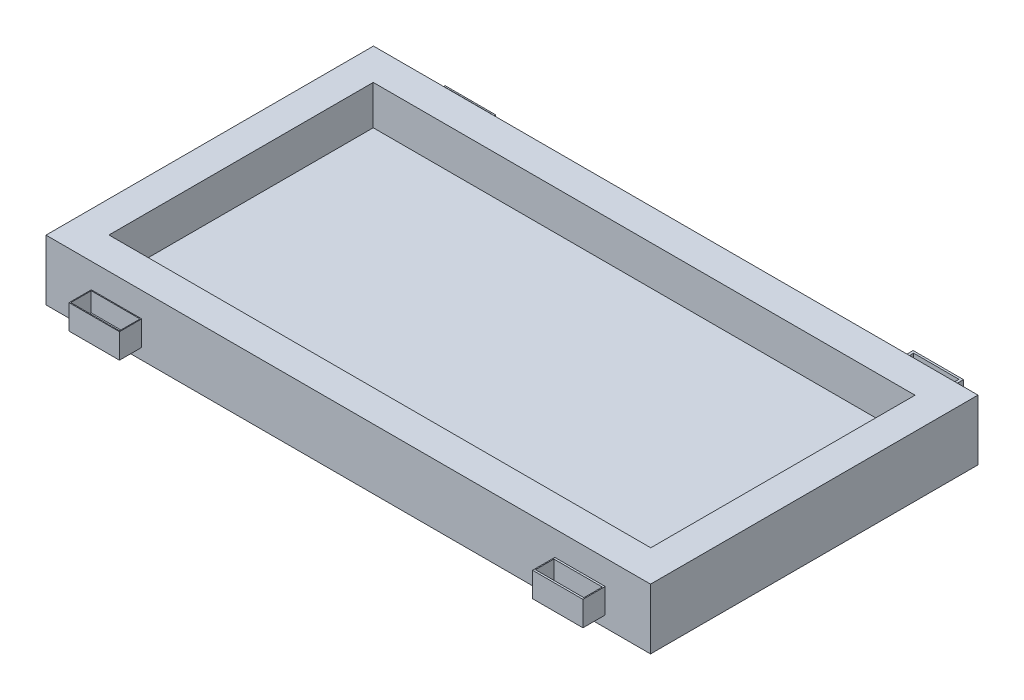
SolidWorks part; units mm, degrees
ref_plane "Front Plane" through (0, 0, 0) normal (0, 0, 1) x (1, 0, 0)
ref_plane "Top Plane" through (0, 0, 0) normal (0, 1, 0) x (1, 0, 0)
ref_plane "Right Plane" through (0, 0, 0) normal (1, 0, 0) x (0, 0, -1)
sketch "Sketch1" plane through (0, 0, 0) normal (0, 1, 0) x (1, 0, 0)
  line L1 (-600, -325) -> (600, -325)
  line L2 (-600, -325) -> (-600, 325)
  line L3 (-600, 325) -> (600, 325)
  line L4 (600, -325) -> (600, 325)
  line L5 (-600, -325) -> (600, 325) construction
  line L6 (-600, 325) -> (600, -325) construction
  point P0 (0, 0)
  dimension "D1" = 1200
  dimension "D2" = 650
extrude "Boss-Extrude1" add sketch "Sketch1" along normal blind 120
sketch "Sketch2" plane through (0, 120, 0) normal (0, 1, 0) x (1, 0, 0)
  line L0 (600, 325) -> (-600, 325) construction
  line L1 (510, 325) -> (410, 325)
  line L2 (510, 325) -> (510, 386.2407)
  line L3 (510, 386.2407) -> (410, 386.2407)
  line L4 (410, 325) -> (410, 386.2407)
  line L5 (-600, -325) -> (600, -325) construction
  line L6 (-410, 325) -> (-510, 325)
  line L7 (-410, 325) -> (-410, 377.0601)
  line L8 (-410, 377.0601) -> (-510, 377.0601)
  line L9 (-510, 325) -> (-510, 377.0601)
  line L10 (-410, -325) -> (-510, -325)
  line L11 (-410, -325) -> (-410, -369.191)
  line L12 (-410, -369.191) -> (-510, -369.191)
  line L13 (-510, -325) -> (-510, -369.191)
  line L14 (-600, 325) -> (-600, -325) construction
  line L15 (510, -325) -> (410, -325)
  line L16 (510, -325) -> (510, -369.191)
  line L17 (510, -369.191) -> (410, -369.191)
  line L18 (410, -325) -> (410, -369.191)
  line L19 (600, -325) -> (600, 325) construction
  dimension "D1" = 90
  dimension "D2" = 90
  dimension "D3" = 90
  dimension "D4" = 90
  dimension "D5" = 100
  dimension "D6" = 100
  dimension "D7" = 100
  dimension "D8" = 100
sketch "Sketch6" plane through (0, 120, 0) normal (0, 1, 0) x (1, 0, 0)
  line L1 (-537.7205, 262.3027) -> (537.7205, 262.3027)
  line L2 (-537.7205, 262.3027) -> (-537.7205, -262.3027)
  line L3 (-537.7205, -262.3027) -> (537.7205, -262.3027)
  line L4 (537.7205, 262.3027) -> (537.7205, -262.3027)
  line L5 (-537.7205, 262.3027) -> (537.7205, -262.3027) construction
  line L6 (-537.7205, -262.3027) -> (537.7205, 262.3027) construction
  point P0 (0, 0)
extrude "Cut-Extrude5" cut sketch "Sketch6" against normal blind 78
extrude "Boss-Extrude3" add sketch "Sketch2" against normal blind 98
sketch "Sketch7" plane through (510, 0, 0) normal (1, 0, 0) x (0, 0, -1)
  line L0 (-325, 120) -> (-369.191, 120)
  line L1 (-369.191, 120) -> (-369.191, 71)
  line L2 (-369.191, 22) -> (-369.191, 120) construction
  line L3 (-369.191, 71) -> (-325, 71)
  line L4 (-325, 22) -> (-325, 120) construction
  line L5 (-325, 71) -> (-325, 120)
extrude "Cut-Extrude6" cut sketch "Sketch7" against normal through all both and the other way through all
sketch "Sketch8" plane through (510, 0, 0) normal (1, 0, 0) x (0, 0, -1)
  line L0 (325, 120) -> (386.2407, 120)
  line L1 (386.2407, 120) -> (386.2407, 71)
  line L2 (386.2407, 22) -> (386.2407, 120) construction
  line L3 (386.2407, 71) -> (325, 71)
  line L4 (325, 22) -> (325, 120) construction
  line L5 (325, 71) -> (325, 120)
extrude "Cut-Extrude7" cut sketch "Sketch8" against normal through all both
sketch "Sketch10" plane through (0, 71, 0) normal (0, 1, 0) x (1, 0, 0)
  line L0 (-460, -369.191) -> (-460, 451.273) construction
  line L1 (-510, -369.191) -> (-410, -369.191) construction
  line L2 (-460, 451.273) -> (460, -369.191) construction
  line L3 (410, -369.191) -> (510, -369.191) construction
  line L4 (460, -369.191) -> (460, 535.0864) construction
  line L5 (-510, -347.0955) -> (510, -347.0955) construction
  line L6 (-510, -325) -> (-510, -369.191) construction
  line L7 (510, -369.191) -> (510, -325) construction
  line L8 (510, -347.0955) -> (510, 355.6203) construction
  line L9 (510, 325) -> (510, 386.2407) construction
  line L10 (510, 355.6203) -> (-604.2719, 355.6203) construction
  line L12 (-508.4233, -326.805) -> (-411.5767, -326.805)
  line L13 (-508.4233, -326.805) -> (-508.4233, -367.386)
  line L14 (-508.4233, -367.386) -> (-411.5767, -367.386)
  line L15 (-411.5767, -326.805) -> (-411.5767, -367.386)
  line L16 (-508.4233, -326.805) -> (-411.5767, -367.386) construction
  line L17 (-508.4233, -367.386) -> (-411.5767, -326.805) construction
  line L18 (411.9109, -328.7576) -> (508.0891, -328.7576)
  line L19 (411.9109, -328.7576) -> (411.9109, -365.4334)
  line L20 (411.9109, -365.4334) -> (508.0891, -365.4334)
  line L21 (508.0891, -328.7576) -> (508.0891, -365.4334)
  line L22 (411.9109, -328.7576) -> (508.0891, -365.4334) construction
  line L23 (411.9109, -365.4334) -> (508.0891, -328.7576) construction
  line L24 (415.0303, 382.2693) -> (504.9697, 382.2693)
  line L25 (415.0303, 382.2693) -> (415.0303, 328.9714)
  line L26 (415.0303, 328.9714) -> (504.9697, 328.9714)
  line L27 (504.9697, 382.2693) -> (504.9697, 328.9714)
  line L28 (415.0303, 382.2693) -> (504.9697, 328.9714) construction
  line L29 (415.0303, 328.9714) -> (504.9697, 382.2693) construction
  line L30 (-506.7113, 374.453) -> (-413.2887, 374.453)
  line L31 (-506.7113, 374.453) -> (-506.7113, 336.7877)
  line L32 (-506.7113, 336.7877) -> (-413.2887, 336.7877)
  line L33 (-413.2887, 374.453) -> (-413.2887, 336.7877)
  line L34 (-506.7113, 374.453) -> (-413.2887, 336.7877) construction
  line L35 (-506.7113, 336.7877) -> (-413.2887, 374.453) construction
  point P14 (-460, -347.0955)
  point P23 (460, -347.0955)
  point P28 (460, 355.6203)
  point P33 (-460, 355.6203)
extrude "Cut-Extrude9" cut sketch "Sketch10" against normal blind 38
sketch "Sketch11" plane through (0, 33, 0) normal (0, 1, 0) x (1, 0, 0)
  circle A0 centre (-462.3072, 358.1204) radius 12.6568
  circle A1 centre (-462.3072, -349.1829) radius 13.6246
  circle A2 centre (463.4093, -349.1829) radius 12.3183
  circle A3 centre (467.3679, 358.1204) radius 17.1623
extrude "Cut-Extrude10" cut sketch "Sketch11" along normal through all both and the other way through all
equation "\"h\"=98"
